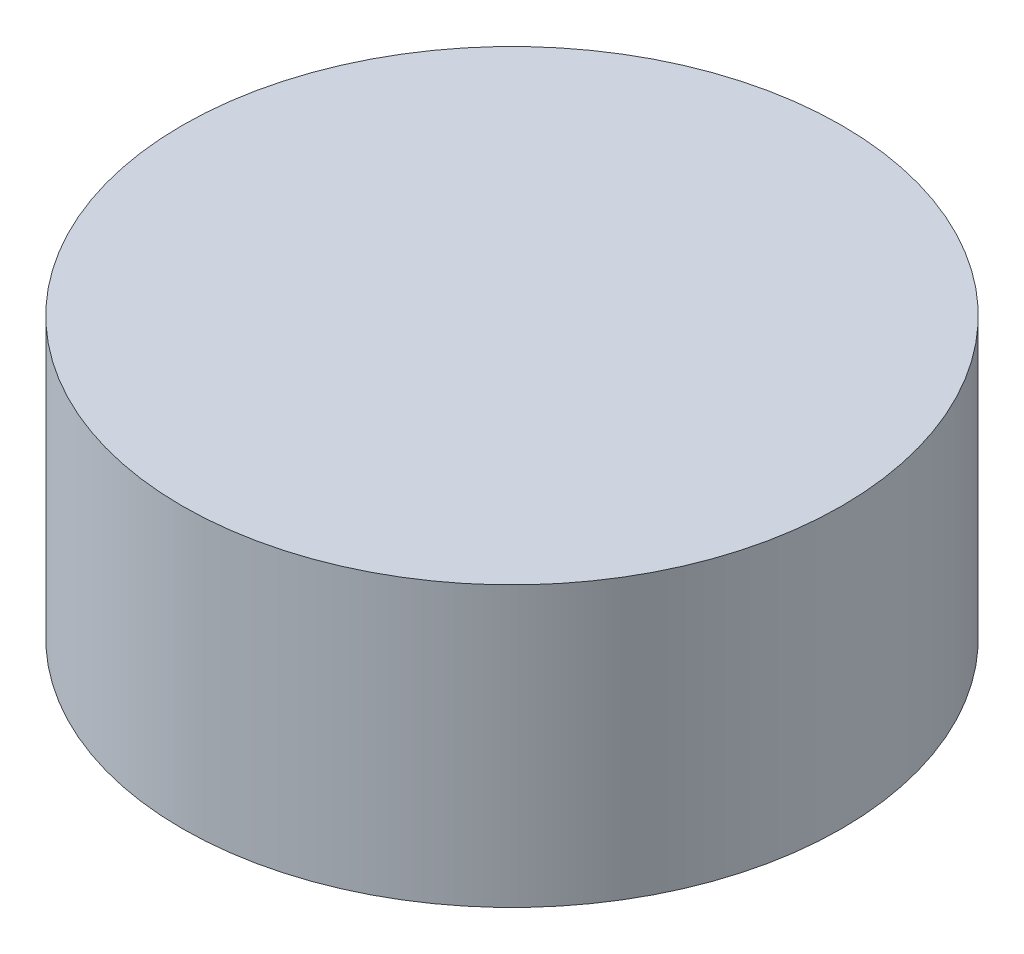
SolidWorks part; units mm, degrees
ref_plane "Front Plane" through (0, 0, 0) normal (0, 0, 1) x (1, 0, 0)
ref_plane "Top Plane" through (0, 0, 0) normal (0, 1, 0) x (1, 0, 0)
ref_plane "Right Plane" through (0, 0, 0) normal (1, 0, 0) x (0, 0, -1)
other "Bounding Box"
ref_plane "Default Plane" through (-8.9266, -12.7485, 0) normal (-0.1736, 0.9848, 0) x (0.9848, 0.1736, 0)
sketch "Sketch1" plane through (0, 0, 0) normal (0, 1, 0) x (1, 0, 0)
  circle A0 centre (0, 0) radius 29.5
  dimension "D1" = 59
extrude "Boss-Extrude1" add sketch "Sketch1" along normal mid plane 25
